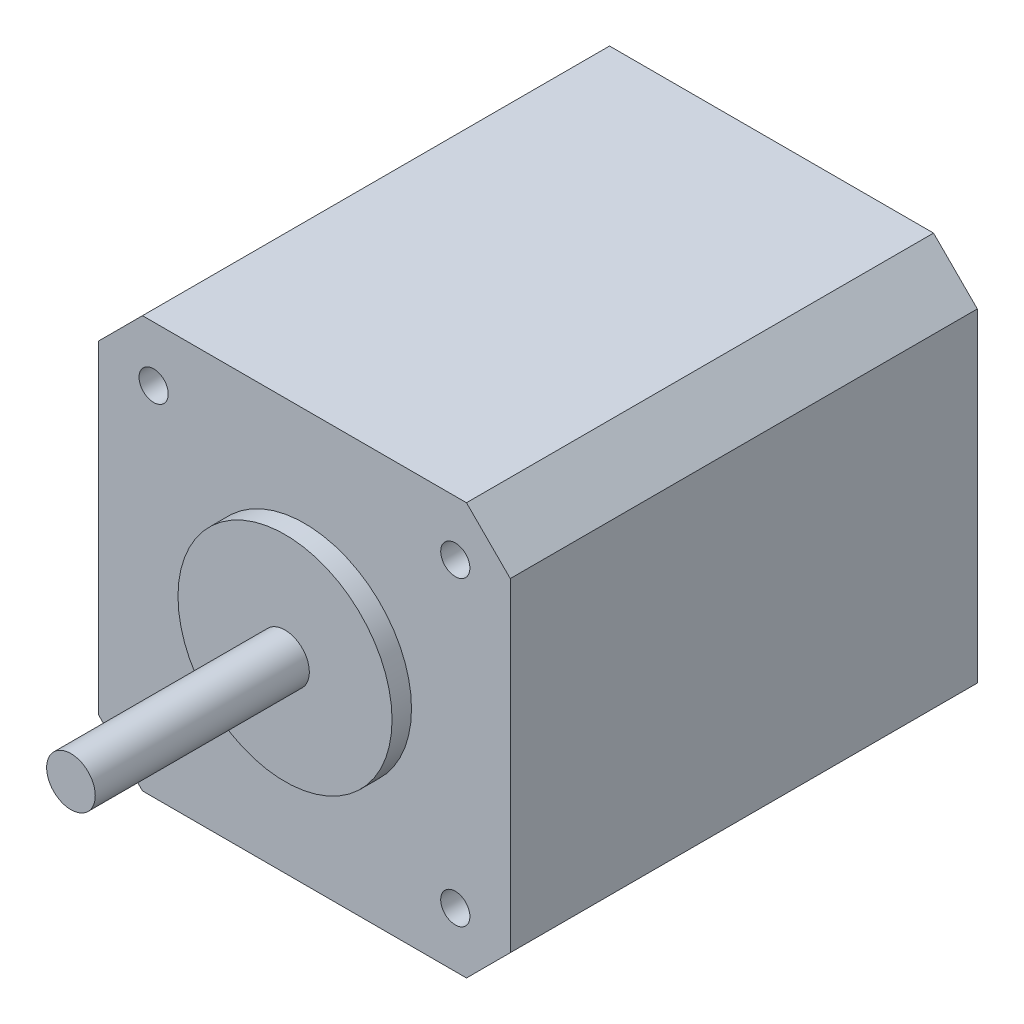
SolidWorks part; units mm, degrees
ref_plane "Front Plane" through (0, 0, 0) normal (0, 0, 1) x (1, 0, 0)
ref_plane "Top Plane" through (0, 0, 0) normal (0, 1, 0) x (1, 0, 0)
ref_plane "Right Plane" through (0, 0, 0) normal (1, 0, 0) x (0, 0, -1)
sketch "Sketch1" plane through (0, 0, 0) normal (0, 0, 1) x (1, 0, 0)
  line L0 (0, 0) -> (0, 21.15) construction
  line L1 (21.15, 21.15) -> (-21.15, 21.15)
  line L2 (21.15, 21.15) -> (21.15, -21.15)
  line L3 (21.15, -21.15) -> (-21.15, -21.15)
  line L4 (-21.15, 21.15) -> (-21.15, -21.15)
  line L5 (21.15, 21.15) -> (-21.15, -21.15) construction
  line L6 (21.15, -21.15) -> (-21.15, 21.15) construction
  line L7 (0, 0) -> (21.15, 0) construction
  circle A0 centre (-15.5, 15.5) radius 1.5
  circle A1 centre (15.5, 15.5) radius 1.5
  circle A2 centre (-15.5, -15.5) radius 1.5
  circle A3 centre (15.5, -15.5) radius 1.5
  point P0 (0, 0)
  dimension "D2" = 31
  dimension "D3" = 3
  dimension "D1" = 42.3
extrude "Boss-Extrude1" add sketch "Sketch1" along normal blind 48
sketch "Sketch2" plane through (0, 0, 48) normal (0, 0, 1) x (1, 0, 0)
  circle A0 centre (0, 0) radius 11
  dimension "D1" = 22
extrude "Boss-Extrude2" add sketch "Sketch2" along normal blind 2
sketch "Sketch3" plane through (0, 0, 50) normal (0, 0, 1) x (1, 0, 0)
  circle A0 centre (0, 0) radius 2.5
  dimension "D1" = 5
extrude "Boss-Extrude3" add sketch "Sketch3" along normal blind 22
chamfer "Chamfer1" distance 4.5 angle 45 4 edges at (21.15, -21.15, 24) (-21.15, -21.15, 24) (-21.15, 21.15, 24) (21.15, 21.15, 24)
